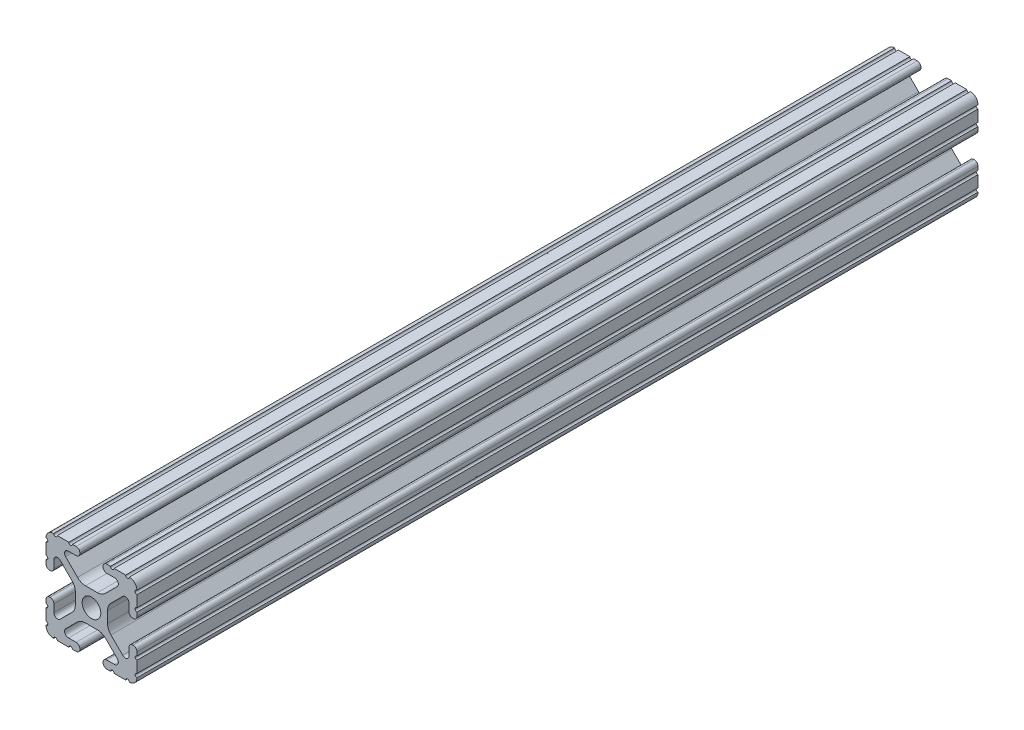
SolidWorks part; units mm, degrees
ref_plane "Front" through (0, 0, 0) normal (0, 0, 1) x (1, 0, 0)
ref_plane "Top" through (0, 0, 0) normal (0, 1, 0) x (1, 0, 0)
ref_plane "Right" through (0, 0, 0) normal (1, 0, 0) x (0, 0, -1)
sketch "Sketch1" plane through (0, 0, 0) normal (0, 0, 1) x (1, 0, 0)
  line L0 (-7.5107, 9.4563) -> (7.5107, 9.4563) construction
  line L1 (-7.4968, -9.4098) -> (7.4968, -9.4098) construction
  line L88 (-7.1797, -8.6452) -> (-3.9523, -5.4237)
  line L89 (-1.7093, -4.4958) -> (1.7093, -4.4958)
  line L90 (3.9523, -5.4237) -> (7.1797, -8.6452)
  line L91 (6.4164, -10.4902) -> (4.2875, -10.4902)
  line L92 (3.2385, -11.5392) -> (3.2385, -11.651)
  line L93 (4.2875, -12.7) -> (5.3171, -12.7)
  line L94 (6.3331, -12.7) -> (9.5504, -12.7)
  line L95 (12.7, -9.5504) -> (12.7, -6.3331)
  line L96 (12.7, -5.3171) -> (12.7, -4.2875)
  line L97 (11.651, -3.2385) -> (11.5392, -3.2385)
  line L98 (10.4902, -4.2875) -> (10.4902, -6.4021)
  line L99 (8.7371, -7.1294) -> (5.441, -3.8408)
  line L100 (4.5085, -1.5932) -> (4.5085, 1.5932)
  line L101 (5.441, 3.8408) -> (8.7371, 7.1294)
  line L102 (10.4902, 6.4021) -> (10.4902, 4.2875)
  line L103 (11.5392, 3.2385) -> (11.651, 3.2385)
  line L104 (12.7, 4.2875) -> (12.7, 5.3171)
  line L105 (12.7, 6.3331) -> (12.7, 9.5504)
  line L106 (9.5504, 12.7) -> (6.3331, 12.7)
  line L107 (5.3171, 12.7) -> (4.2875, 12.7)
  line L108 (3.2385, 11.651) -> (3.2385, 11.5392)
  line L109 (4.2875, 10.4902) -> (6.4768, 10.4902)
  line L110 (7.207, 8.7244) -> (3.8983, 5.4232)
  line L111 (1.6558, 4.4958) -> (-1.6558, 4.4958)
  line L112 (-3.8983, 5.4232) -> (-7.207, 8.7244)
  line L113 (-6.4768, 10.4902) -> (-4.2875, 10.4902)
  line L114 (-3.2385, 11.5392) -> (-3.2385, 11.651)
  line L115 (-4.2875, 12.7) -> (-5.3171, 12.7)
  line L116 (-6.3331, 12.7) -> (-9.5504, 12.7)
  line L117 (-12.7, 9.5504) -> (-12.7, 6.3331)
  line L118 (-12.7, 5.3171) -> (-12.7, 4.2875)
  line L119 (-11.651, 3.2385) -> (-11.5392, 3.2385)
  line L120 (-10.4902, 4.2875) -> (-10.4902, 6.4021)
  line L121 (-8.7371, 7.1294) -> (-5.441, 3.8408)
  line L122 (-4.5085, 1.5932) -> (-4.5085, -1.5932)
  line L123 (-5.441, -3.8408) -> (-8.7371, -7.1294)
  line L124 (-10.4902, -6.4021) -> (-10.4902, -4.2875)
  line L125 (-11.5392, -3.2385) -> (-11.651, -3.2385)
  line L126 (-12.7, -4.2875) -> (-12.7, -5.3171)
  line L127 (-12.7, -6.3331) -> (-12.7, -9.5504)
  line L128 (-9.5504, -12.7) -> (-6.3331, -12.7)
  line L129 (-5.3171, -12.7) -> (-4.2875, -12.7)
  line L130 (-3.2385, -11.651) -> (-3.2385, -11.5392)
  line L131 (-4.2875, -10.4902) -> (-6.4164, -10.4902)
  circle A1 centre (0, 0) radius 2.6035
  arc A104 (-7.1797, -8.6452) -> (-6.4164, -10.4902) centre (-6.4164, -9.4098) ccw
  arc A105 (-1.7093, -4.4958) -> (-3.9523, -5.4237) centre (-1.7093, -7.6708) ccw
  arc A106 (3.9523, -5.4237) -> (1.7093, -4.4958) centre (1.7093, -7.6708) ccw
  arc A107 (6.4164, -10.4902) -> (7.1797, -8.6452) centre (6.4164, -9.4098) ccw
  arc A108 (4.2875, -10.4902) -> (3.2385, -11.5392) centre (4.2875, -11.5392) ccw
  arc A109 (3.2385, -11.651) -> (4.2875, -12.7) centre (4.2875, -11.651) ccw
  arc A110 (6.3331, -12.7) -> (5.3171, -12.7) centre (5.8251, -12.7) ccw
  arc A111 (10.5664, -12.6998) -> (9.5504, -12.7) centre (10.0584, -12.7) ccw
  arc A112 (10.5664, -12.6998) -> (12.6998, -10.5664) centre (10.5918, -10.5918) ccw
  arc A113 (12.7, -9.5504) -> (12.6998, -10.5664) centre (12.7, -10.0584) ccw
  arc A114 (12.7, -5.3171) -> (12.7, -6.3331) centre (12.7, -5.8251) ccw
  arc A115 (12.7, -4.2875) -> (11.651, -3.2385) centre (11.651, -4.2875) ccw
  arc A116 (11.5392, -3.2385) -> (10.4902, -4.2875) centre (11.5392, -4.2875) ccw
  arc A117 (8.7371, -7.1294) -> (10.4902, -6.4021) centre (9.4628, -6.4021) ccw
  arc A118 (4.5085, -1.5932) -> (5.441, -3.8408) centre (7.6835, -1.5932) ccw
  arc A119 (5.441, 3.8408) -> (4.5085, 1.5932) centre (7.6835, 1.5932) ccw
  arc A120 (10.4902, 6.4021) -> (8.7371, 7.1294) centre (9.4628, 6.4021) ccw
  arc A121 (10.4902, 4.2875) -> (11.5392, 3.2385) centre (11.5392, 4.2875) ccw
  arc A122 (11.651, 3.2385) -> (12.7, 4.2875) centre (11.651, 4.2875) ccw
  arc A123 (12.7, 6.3331) -> (12.7, 5.3171) centre (12.7, 5.8251) ccw
  arc A124 (12.6998, 10.5664) -> (12.7, 9.5504) centre (12.7, 10.0584) ccw
  arc A125 (12.6998, 10.5664) -> (10.5664, 12.6998) centre (10.5918, 10.5918) ccw
  arc A126 (9.5504, 12.7) -> (10.5664, 12.6998) centre (10.0584, 12.7) ccw
  arc A127 (5.3171, 12.7) -> (6.3331, 12.7) centre (5.8251, 12.7) ccw
  arc A128 (4.2875, 12.7) -> (3.2385, 11.651) centre (4.2875, 11.651) ccw
  arc A129 (3.2385, 11.5392) -> (4.2875, 10.4902) centre (4.2875, 11.5392) ccw
  arc A130 (7.207, 8.7244) -> (6.4768, 10.4902) centre (6.4768, 9.4563) ccw
  arc A131 (1.6558, 4.4958) -> (3.8983, 5.4232) centre (1.6558, 7.6708) ccw
  arc A132 (-3.8983, 5.4232) -> (-1.6558, 4.4958) centre (-1.6558, 7.6708) ccw
  arc A133 (-6.4768, 10.4902) -> (-7.207, 8.7244) centre (-6.4768, 9.4563) ccw
  arc A134 (-4.2875, 10.4902) -> (-3.2385, 11.5392) centre (-4.2875, 11.5392) ccw
  arc A135 (-3.2385, 11.651) -> (-4.2875, 12.7) centre (-4.2875, 11.651) ccw
  arc A136 (-6.3331, 12.7) -> (-5.3171, 12.7) centre (-5.8251, 12.7) ccw
  arc A137 (-10.5664, 12.6998) -> (-9.5504, 12.7) centre (-10.0584, 12.7) ccw
  arc A138 (-10.5664, 12.6998) -> (-12.6998, 10.5664) centre (-10.5918, 10.5918) ccw
  arc A139 (-12.7, 9.5504) -> (-12.6998, 10.5664) centre (-12.7, 10.0584) ccw
  arc A140 (-12.7, 5.3171) -> (-12.7, 6.3331) centre (-12.7, 5.8251) ccw
  arc A141 (-12.7, 4.2875) -> (-11.651, 3.2385) centre (-11.651, 4.2875) ccw
  arc A142 (-11.5392, 3.2385) -> (-10.4902, 4.2875) centre (-11.5392, 4.2875) ccw
  arc A143 (-8.7371, 7.1294) -> (-10.4902, 6.4021) centre (-9.4628, 6.4021) ccw
  arc A144 (-4.5085, 1.5932) -> (-5.441, 3.8408) centre (-7.6835, 1.5932) ccw
  arc A145 (-5.441, -3.8408) -> (-4.5085, -1.5932) centre (-7.6835, -1.5932) ccw
  arc A146 (-10.4902, -6.4021) -> (-8.7371, -7.1294) centre (-9.4628, -6.4021) ccw
  arc A147 (-10.4902, -4.2875) -> (-11.5392, -3.2385) centre (-11.5392, -4.2875) ccw
  arc A148 (-11.651, -3.2385) -> (-12.7, -4.2875) centre (-11.651, -4.2875) ccw
  arc A149 (-12.7, -6.3331) -> (-12.7, -5.3171) centre (-12.7, -5.8251) ccw
  arc A150 (-12.6998, -10.5664) -> (-12.7, -9.5504) centre (-12.7, -10.0584) ccw
  arc A151 (-12.6998, -10.5664) -> (-10.5664, -12.6998) centre (-10.5918, -10.5918) ccw
  arc A152 (-9.5504, -12.7) -> (-10.5664, -12.6998) centre (-10.0584, -12.7) ccw
  arc A153 (-5.3171, -12.7) -> (-6.3331, -12.7) centre (-5.8251, -12.7) ccw
  arc A154 (-4.2875, -12.7) -> (-3.2385, -11.651) centre (-4.2875, -11.651) ccw
  arc A155 (-3.2385, -11.5392) -> (-4.2875, -10.4902) centre (-4.2875, -11.5392) ccw
extrude "Boss-Extrude1" add sketch "Sketch1" along normal mid plane 234.95
